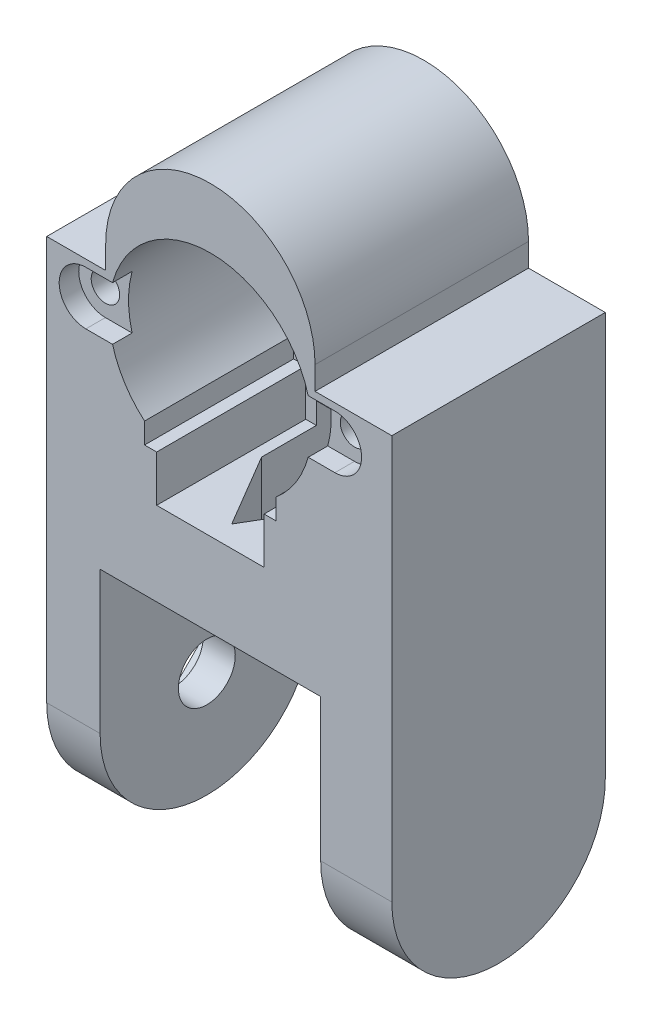
SolidWorks part; units mm, degrees
ref_plane "Front Plane" through (0, 0, 0) normal (0, 0, 1) x (1, 0, 0)
ref_plane "Top Plane" through (0, 0, 0) normal (0, 1, 0) x (1, 0, 0)
ref_plane "Right Plane" through (0, 0, 0) normal (1, 0, 0) x (0, 0, -1)
sketch "Sketch2" plane through (0, 0, 0) normal (0, 0, 1) x (1, 0, 0)
  line L0 (-7.55, 18.2411) -> (-7.55, 14.75)
  line L1 (-7.55, 14.75) -> (7.55, 14.75)
  line L2 (7.55, 14.75) -> (7.55, 18.2411)
  line L3 (7.55, 18.2411) -> (9.25, 18.2411)
  line L4 (9.25, 18.2411) -> (9.25, 21.1603)
  line L5 (-7.55, 18.2411) -> (-9.25, 18.2411)
  line L6 (-9.25, 18.2411) -> (-9.25, 21.1603)
  line L7 (-14.7095, 40) -> (-23, 40)
  line L8 (-23, 40) -> (-23, 0)
  line L10 (14.7095, 40) -> (23, 40)
  line L11 (23, 40) -> (23, 0)
  line L13 (-23, 0) -> (23, 0)
  arc A0 (14.7095, 40) -> (-14.7095, 40) centre (0, 40) ccw
  arc A4 (9.25, 21.1603) -> (-9.25, 21.1603) centre (0, 32) ccw
  point P6 (0, 14.75)
  point P15 (0, 0)
  dimension "D1" = 8.2905
  dimension "D12" = 3.4911
  dimension "D16" = 14.25
  dimension "D17" = 14.7095
  dimension "D2" = 8.2905
  dimension "D3" = 25.25
  dimension "D4" = 40
  dimension "D5" = 0
  dimension "D6" = 0
  dimension "D7" = 46
  dimension "D9" = 2.9191
  dimension "D10" = 1.7
  dimension "D11" = 1.7
  dimension "D13" = 15.1
  dimension "D14" = 2.9191
  dimension "D15" = 3.4911
extrude "Boss-Extrude1" add sketch "Sketch2" along normal blind 20.95
sketch "Sketch3" plane through (0, 0, 0) normal (0, 0, 1) x (1, 0, 0)
  line L7 (-14.7095, 40) -> (-23, 40)
  line L8 (-23, 40) -> (-23, 0)
  line L9 (14.7095, 40) -> (23, 40)
  line L10 (23, 40) -> (23, 0)
  line L11 (-23, 0) -> (23, 0)
  line L12 (23, 40) -> (14.7095, 40) construction
  line L13 (-23, 40) -> (-23, 0) construction
  line L17 (-23, 0) -> (23, 0) construction
  line L19 (23, 0) -> (23, 40) construction
  arc A0 (14.7095, 40) -> (-14.7095, 40) centre (0, 40) ccw
  arc A1 (14.7095, 40) -> (-14.7095, 40) centre (0, 40) ccw construction
  dimension "D1" = 0
extrude "Boss-Extrude2" add sketch "Sketch3" against normal blind 9.05
sketch "Sketch6" plane through (0, 0, 20.95) normal (0, 0, 1) x (1, 0, 0)
  line L0 (-14.7095, 40) -> (-23, 40) construction
  line L1 (-23, 40) -> (-23, 0) construction
  line L2 (23, 40) -> (14.7095, 40) construction
  line L3 (23, 0) -> (23, 40) construction
  circle A0 centre (-17.5, 32) radius 2
  circle A1 centre (17.5, 32) radius 2
  dimension "D1" = 8
  dimension "D2" = 5.5
  dimension "D3" = 4
  dimension "D4" = 8
  dimension "D5" = 5.5
  dimension "D6" = 4
extrude "Cut-Extrude2" cut sketch "Sketch6" against normal blind 10
sketch "Sketch7" plane through (0, 0, 20.95) normal (0, 0, 1) x (1, 0, 0)
  line L0 (-17.5, 32) -> (17.5, 32) construction
  line L3 (-17.5, 35.75) -> (17.5, 35.75)
  line L4 (-17.5, 28.25) -> (17.5, 28.25)
  arc A2 (-17.5, 35.75) -> (-17.5, 28.25) centre (-17.5, 32) ccw
  arc A3 (17.5, 28.25) -> (17.5, 35.75) centre (17.5, 32) ccw
  circle A4 centre (-17.5, 32) radius 2 construction
  circle A5 centre (-17.5, 32) radius 2 construction
  circle A6 centre (17.5, 32) radius 2 construction
  point P2 (0, 32)
  dimension "D2" = 7.5
  dimension "D3" = 1.75
  dimension "D4" = 1.75
  dimension "D1" = 3.75
extrude "Cut-Extrude3" cut sketch "Sketch7" against normal blind 2.75
sketch "Sketch8" plane through (0, 0, 20.95) normal (0, 0, 1) x (1, 0, 0)
  line L0 (-14.7095, 40) -> (-23, 40) construction
  line L1 (-14.7095, 40) -> (-23, 40)
  line L2 (-14.7095, 40) -> (-14.7095, 36.75)
  line L3 (-14.7095, 36.75) -> (-23, 36.75)
  line L4 (-23, 40) -> (-23, 36.75)
  line L5 (14.7095, 40) -> (23, 40)
  line L6 (14.7095, 40) -> (14.7095, 36.75)
  line L7 (14.7095, 36.75) -> (23, 36.75)
  line L8 (23, 40) -> (23, 36.75)
  line L9 (-23, 40) -> (-23, 0) construction
  line L10 (-13.7477, 35.75) -> (-17.5, 35.75) construction
  line L11 (17.5, 35.75) -> (13.7477, 35.75) construction
  line L12 (23, 0) -> (23, 40) construction
  line L13 (23, 40) -> (14.7095, 40) construction
  dimension "D2" = 1
  dimension "D3" = 1
extrude "Cut-Extrude4" cut sketch "Sketch8" along normal through all both and the other way through all
sketch "Sketch11" plane through (0, 0, -9.05) normal (0, 0, -1) x (-1, 0, 0)
  circle A0 centre (0, 40) radius 11.15
  arc A1 (14.7095, 40) -> (-14.7095, 40) centre (0, 40) ccw construction
  dimension "D1" = 22.3
extrude "Bearing Hole" cut sketch "Sketch11" against normal blind 7.3
sketch "Sketch9" plane through (0, 14.75, -19.25) normal (0, 1, 0) x (-1, 0, 0)
  line L0 (7.55, 40.2) -> (-7.55, 40.2) construction
  line L1 (-6.05, 37.7) -> (6.05, 37.7)
  line L2 (-6.05, 37.7) -> (-6.05, 16.2)
  line L3 (-6.05, 16.2) -> (6.05, 16.2)
  line L4 (6.05, 37.7) -> (6.05, 16.2)
  line L8 (-7.55, 40.2) -> (-7.55, 19.25) construction
  line L9 (7.55, 40.2) -> (7.55, 19.25) construction
  line L10 (7.55, 10.2) -> (-7.55, 10.2) construction
  dimension "D1" = 2.5
  dimension "D2" = 1.5
  dimension "D3" = 1.5
  dimension "D4" = 6
extrude "Wire Hole" cut sketch "Sketch9" against normal through all
sketch "Sketch12" plane through (0, 0, 0) normal (0, -1, 0) x (1, 0, 0)
  line L0 (-23, -9.05) -> (23, -9.05) construction
  line L1 (-23, -9.05) -> (23, -9.05)
  line L2 (-23, -9.05) -> (-23, 20.95)
  line L3 (-23, 20.95) -> (23, 20.95)
  line L4 (23, -9.05) -> (23, 20.95)
  line L5 (-23, 20.95) -> (23, 20.95) construction
  line L7 (-23, 20.95) -> (-23, -9.05) construction
  point P4 (0, -9.05)
  dimension "D1" = 0
  dimension "D2" = 0
  dimension "D3" = 0
  dimension "D4" = 0
extrude "Boss-Extrude3" add sketch "Sketch12" along normal blind 0.0001
sketch "Sketch13" plane through (23, 0, 0) normal (1, 0, 0) x (0, 0, -1)
  line L0 (-20.95, -0.0001) -> (-20.95, -20.0001)
  line L1 (9.05, -0.0001) -> (9.05, -20.0001)
  line L6 (9.05, 36.75) -> (-20.95, 36.75)
  line L7 (-20.95, 36.75) -> (-20.95, -0.0001)
  line L8 (-20.95, -0.0001) -> (9.05, -0.0001)
  line L9 (9.05, -0.0001) -> (9.05, 36.75)
  line L12 (-20.95, -0.0001) -> (9.05, -0.0001)
  arc A0 (-20.95, -20.0001) -> (9.05, -20.0001) centre (-5.95, -20.0001) ccw
  dimension "D1" = 0
  dimension "D2" = 20
extrude "Boss-Extrude4" add sketch "Sketch13" against normal blind 7.5
sketch "Sketch14" plane through (-23, 0, 0) normal (-1, 0, 0) x (0, 0, 1)
  line L0 (-9.05, -20.0001) -> (-9.05, -0.0001)
  line L1 (-9.05, -0.0001) -> (20.95, -0.0001)
  line L2 (20.95, -0.0001) -> (20.95, -20.0001)
  arc A0 (-9.05, -20.0001) -> (20.95, -20.0001) centre (5.95, -20.0001) ccw
extrude "Boss-Extrude5" add sketch "Sketch14" against normal blind 7.5
sketch "Sketch21" plane through (23, 0, 0) normal (1, 0, 0) x (0, 0, -1)
  line L0 (-20.95, -20.0001) -> (-20.95, 36.75)
  line L1 (-20.95, 36.75) -> (9.05, 36.75)
  line L2 (9.05, 36.75) -> (9.05, -20.0001)
  arc A0 (-20.95, -20.0001) -> (9.05, -20.0001) centre (-5.95, -20.0001) ccw
extrude "Boss-Extrude9" add sketch "Sketch21" along normal blind 2.5
sketch "Sketch15" plane through (-23, 0, 0) normal (-1, 0, 0) x (0, 0, 1)
  circle A0 centre (5.95, -20.0001) radius 4
extrude "Cut-Extrude5" cut sketch "Sketch15" against normal through all
sketch "Sketch17" plane through (25.5, 0, -23) normal (-1, 0, 0) x (0, 0, 1)
  line L4 (26.7654, -18.5001) -> (31.1346, -18.5001)
  line L5 (26.7654, -21.5001) -> (31.1346, -21.5001)
  arc A10 (26.7654, -18.5001) -> (26.7654, -21.5001) centre (28.95, -20.0001) ccw
  arc A11 (31.1346, -18.5001) -> (31.1346, -21.5001) centre (28.95, -20.0001) cw
  circle A14 centre (28.95, -20.0001) radius 6.1696
  arc A16 (13.95, -20.0001) -> (43.95, -20.0001) centre (28.95, -20.0001) ccw construction
  circle A17 centre (28.95, -20.0001) radius 4 construction
  point P11 (28.95, -35.0001)
  dimension "D1" = 3
  dimension "D2" = 1.5
  dimension "D3" = 2.65
  dimension "D4" = 2.65
extrude "Boss-Extrude6" add sketch "Sketch17" along normal up to surface (10 mm away) up to face at (15.5, -20.0001, 1.95)
sketch "Sketch18" plane through (-23, 0, 0) normal (-1, 0, 0) x (0, 0, 1)
  circle A0 centre (5.95, -20.0001) radius 3.85
  dimension "D1" = 7.7
extrude "Boss-Extrude7" add sketch "Sketch18" against normal offset from surface (14 mm away) 6.5 up to face at (-15.5, -24.0001, 5.95) offset beyond the face yes
sketch "Sketch19" plane through (15.5, 0, 0) normal (-1, 0, 0) x (0, 0, 1)
  circle A0 centre (5.95, -20.0001) radius 4.675
  dimension "D1" = 9.35
extrude "Cut-Extrude6" cut sketch "Sketch19" against normal blind 2
sketch "Sketch24" plane through (0, 0, -1.75) normal (0, 0, -1) x (-1, 0, 0)
  circle A0 centre (0, 40) radius 3.5
  dimension "D1" = 7
extrude "Cut-Extrude7" cut sketch "Sketch24" against normal through all
fillet "Fillet1" radius 0.5 1 edges at (-11.15, 40, -9.05)
sketch "Sketch25" plane through (25.5, 0, 0) normal (1, 0, 0) x (0, 0, -1)
  line L1 (-10.6075, -17.9723) -> (-1.7642, -17.9723)
  line L2 (-10.6075, -17.9723) -> (-10.6075, -22.8066)
  line L3 (-10.6075, -22.8066) -> (-1.7642, -22.8066)
  line L4 (-1.7642, -17.9723) -> (-1.7642, -22.8066)
extrude "Boss-Extrude10" add sketch "Sketch25" against normal blind 2
sketch "Sketch27" plane through (0, 14.75, 0) normal (0, 1, 0) x (1, 0, 0)
  line L1 (-6.05, -18.45) -> (6.05, -18.45)
  line L2 (-6.05, -18.45) -> (-6.05, 3.05)
  line L3 (-6.05, 3.05) -> (6.05, 3.05)
  line L4 (6.05, -18.45) -> (6.05, 3.05)
extrude "Cut-Extrude8" cut sketch "Sketch27" against normal through all
sketch "Sketch28" plane through (0, -0.0001, 0) normal (0, -1, 0) x (1, 0, 0)
  line L1 (-6.05, -3.05) -> (-6.05, 18.45) construction
  line L2 (6.05, 18.45) -> (6.05, -3.05) construction
  line L4 (-6.05, 7.7) -> (0, 17.95)
  line L5 (0, 17.95) -> (6.05, 7.7)
  line L8 (-6.05, -3.05) -> (6.05, -3.05)
  line L9 (-6.05, 18.45) -> (-6.05, -3.05)
  line L10 (6.05, 18.45) -> (-6.05, 18.45)
  line L11 (6.05, -3.05) -> (6.05, 18.45)
  line L13 (-6.05, 18.45) -> (-6.05, 7.7)
  line L14 (6.05, 18.45) -> (-6.05, 18.45)
  line L15 (6.05, 7.7) -> (6.05, 18.45)
  dimension "D1" = 0
  dimension "D2" = 0.5
extrude "Boss-Extrude11" add sketch "Sketch28" against normal up to surface (14.7501 mm away) up to face at (0, 14.75, 9.85)
sketch "Sketch29" plane through (0, 0, 20.95) normal (0, 0, 1) x (1, 0, 0)
  line L1 (-7.55, 14.75) -> (7.55, 14.75)
  line L2 (-7.55, 14.75) -> (-7.55, 11.75)
  line L3 (-7.55, 11.75) -> (7.55, 11.75)
  line L4 (7.55, 14.75) -> (7.55, 11.75)
  dimension "D1" = 3
extrude "Cut-Extrude9" cut sketch "Sketch29" against normal up to surface (20.95 mm away) up to face at (3.5, 40, 0)
sketch "Sketch30" plane through (-23, 0, 0) normal (-1, 0, 0) x (0, 0, 1)
  circle A0 centre (5.95, -20.0001) radius 4
  dimension "D1" = 8
extrude "Cut-Extrude10" cut sketch "Sketch30" against normal up to surface (14 mm away) up to face at (-9, -23.8501, 5.95)
sketch "Sketch31" plane through (-23, 0, 0) normal (-1, 0, 0) x (0, 0, 1)
  line L3 (5.95, -10.0001) -> (15.95, -20.0001)
  line L4 (15.95, -20.0001) -> (5.95, -30.0001)
  line L5 (5.95, -30.0001) -> (-4.05, -20.0001)
  line L6 (-4.05, -20.0001) -> (5.95, -10.0001)
  line L7 (3.7654, -21.5001) -> (8.1346, -21.5001) construction
  arc A0 (8.1346, -21.5001) -> (8.1346, -18.5001) centre (5.95, -20.0001) ccw construction
  point P13 (5.95, -21.5001)
  point P18 (8.6, -20.0001)
  dimension "D1" = 10
  dimension "D2" = 10
  dimension "D3" = 0
  dimension "D4" = 10
  dimension "D5" = 10
extrude "Cut-Extrude11" cut sketch "Sketch31" against normal blind 3
